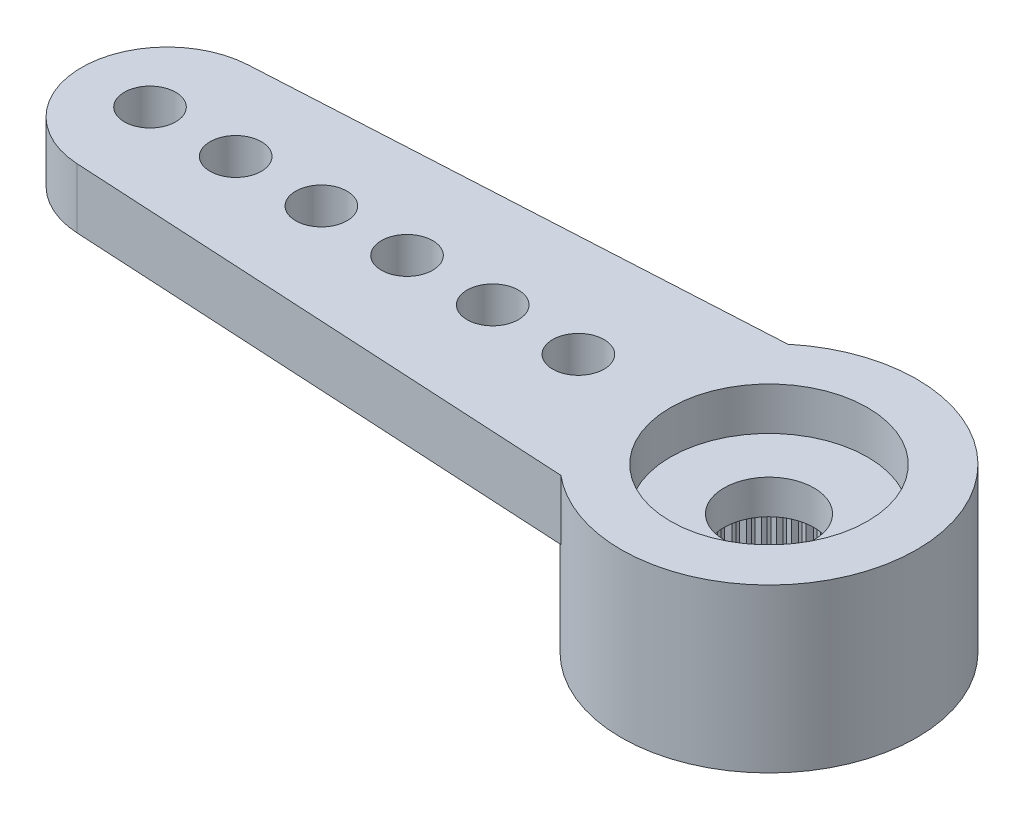
SolidWorks part; units mm, degrees
material "PVC Rígido"
ref_plane "Plano frontal" through (0, 0, 0) normal (0, 0, 1) x (1, 0, 0)
ref_plane "Plano superior" through (0, 0, 0) normal (0, 1, 0) x (1, 0, 0)
ref_plane "Plano direito" through (0, 0, 0) normal (1, 0, 0) x (0, 0, -1)
sketch "Esboço1" plane through (0, 0, 0) normal (0, 1, 0) x (1, 0, 0)
  line L0 (0, 0) -> (-14.05, 0) construction
  line L1 (-14.1591, 1.997) -> (-2.2091, 2.65)
  line L2 (-2.2091, -2.65) -> (-14.1591, -1.997)
  arc A0 (-2.2091, -2.65) -> (-2.2091, 2.65) centre (0, 0) ccw
  arc A1 (-14.1591, 1.997) -> (-14.1591, -1.997) centre (-14.05, 0) ccw
  dimension "D1" = 6.9
  dimension "D2" = 4
  dimension "D3" = 19.5
  dimension "D4" = 5.3
extrude "Ressalto-extrusão1" add sketch "Esboço1" against normal blind 1.4
sketch "Esboço2" plane through (0, -1.4, 0) normal (0, -1, 0) x (1, 0, 0)
  arc A0 (-2.2091, -2.65) -> (-2.2091, 2.65) centre (0, 0) ccw construction
  circle A1 centre (0, 0) radius 3.45
extrude "Ressalto-extrusão2" add sketch "Esboço2" along normal offset from surface (2.4 mm away) 3.8 up to face at (-7.242, 0, 0)
hole_wizard "Furo4" positions "Esboço9" profile "Esboço10" legacy end condition through all
sketch "Esboço9" plane through (0, 0, 0) normal (0, 1, 0) x (1, 0, 0)
  line L1 (-14.45, 0) -> (0, 0) construction
  arc A2 (-14.1591, 1.997) -> (-14.1591, -1.997) centre (-14.05, 0) ccw construction
  point P0 (-14.45, 0)
  point P19 (-16.05, 0)
  dimension "D1" = 1.6
sketch "Esboço10" plane through (-14.45, 0, 0) normal (1, 0, 0) x (0, 0, 1)
  line L0 (0, 0) -> (0, 3.8)
  line L1 (0, 3.8) -> (0.6, 3.8)
  line L2 (0.6, 3.8) -> (0.6, 0)
  line L3 (0.6, 0) -> (0, 0)
  line L4 (0, 110) -> (0, -10) construction
  dimension "Diameter" = 1.2
  dimension "Depth" = 3.8
pattern_linear "Padrão linear1" count 6 spacing 2 along (1, 0, 0) of "Furo4"
hole_wizard "Furo1" positions "Esboço3" profile "Esboço4" legacy
sketch "Esboço3" plane through (0, -3.8, 0) normal (0, -1, 0) x (-1, 0, 0)
  point P0 (0, 0)
sketch "Esboço4" plane through (0, -3.8, 0) normal (1, 0, 0) x (0, 0, -1)
  line L0 (0, 0) -> (0, 2)
  line L1 (0, 2) -> (2.475, 2)
  line L2 (2.475, 2) -> (2.475, 0)
  line L3 (2.475, 0) -> (0, 0)
  line L4 (0, 110) -> (0, -10) construction
  dimension "Diameter" = 4.95
  dimension "Depth" = 2
hole_wizard "Furo2" positions "Esboço5" profile "Esboço6" legacy
sketch "Esboço5" plane through (0, 0, 0) normal (0, 1, 0) x (1, 0, 0)
  point P0 (0, 0)
sketch "Esboço6" plane through (0, 0, 0) normal (1, 0, 0) x (0, 0, 1)
  line L0 (0, 0) -> (0, 1)
  line L1 (0, 1) -> (2.3, 1)
  line L2 (2.3, 1) -> (2.3, 0)
  line L3 (2.3, 0) -> (0, 0)
  line L4 (0, 110) -> (0, -10) construction
  dimension "Diameter" = 4.6
  dimension "Depth" = 1
hole_wizard "Furo3" positions "Esboço7" profile "Esboço8" legacy end condition through all
sketch "Esboço7" plane through (0, 0, 0) normal (0, 1, 0) x (1, 0, 0)
  point P0 (0, 0)
sketch "Esboço8" plane through (0, 0, 0) normal (1, 0, 0) x (0, 0, 1)
  line L0 (0, 0) -> (0, 3.8)
  line L1 (0, 3.8) -> (1.05, 3.8)
  line L2 (1.05, 3.8) -> (1.05, 0)
  line L3 (1.05, 0) -> (0, 0)
  line L4 (0, 110) -> (0, -10) construction
  dimension "Diameter" = 2.1
  dimension "Depth" = 3.8
sketch "Esboço11" plane through (0, -3.8, 0) normal (0, -1, 0) x (1, 0, 0)
  line L0 (-0.0981, 2.4731) -> (0, 2.375)
  line L1 (0, 2.375) -> (0.0981, 2.4731)
  line L2 (0, 0) -> (0, 2.475) construction
  circle A0 centre (0, 0) radius 2.375 construction
  circle A1 centre (0, 0) radius 2.475
  arc A2 (0.0981, 2.4731) -> (-0.0981, 2.4731) centre (0, 0) ccw
  dimension "D3" = 4.75
  dimension "D2" = 0.1
  dimension "D1" = 0
extrude "Ressalto-extrusão3" add sketch "Esboço11" against normal up to surface (2 mm away) up to face at (0, -1.8, 1.05)
pattern_circular "PadrãoCircular1" count 60 over 360 about axis through (0, 0, 0) along (0, 1, 0) of "Ressalto-extrusão3"
sketch "ｽｹｯﾁ1" plane through (0, -3.8, 0) normal (0, -1, 0) x (1, 0, 0)
  line L0 (3.45, 0) -> (-3.45, 0) construction
  line L1 (0, 0) -> (3.45, 0) construction
  circle A2 centre (0, 0) radius 3.45 construction
  point P6 (3.45, 0)
